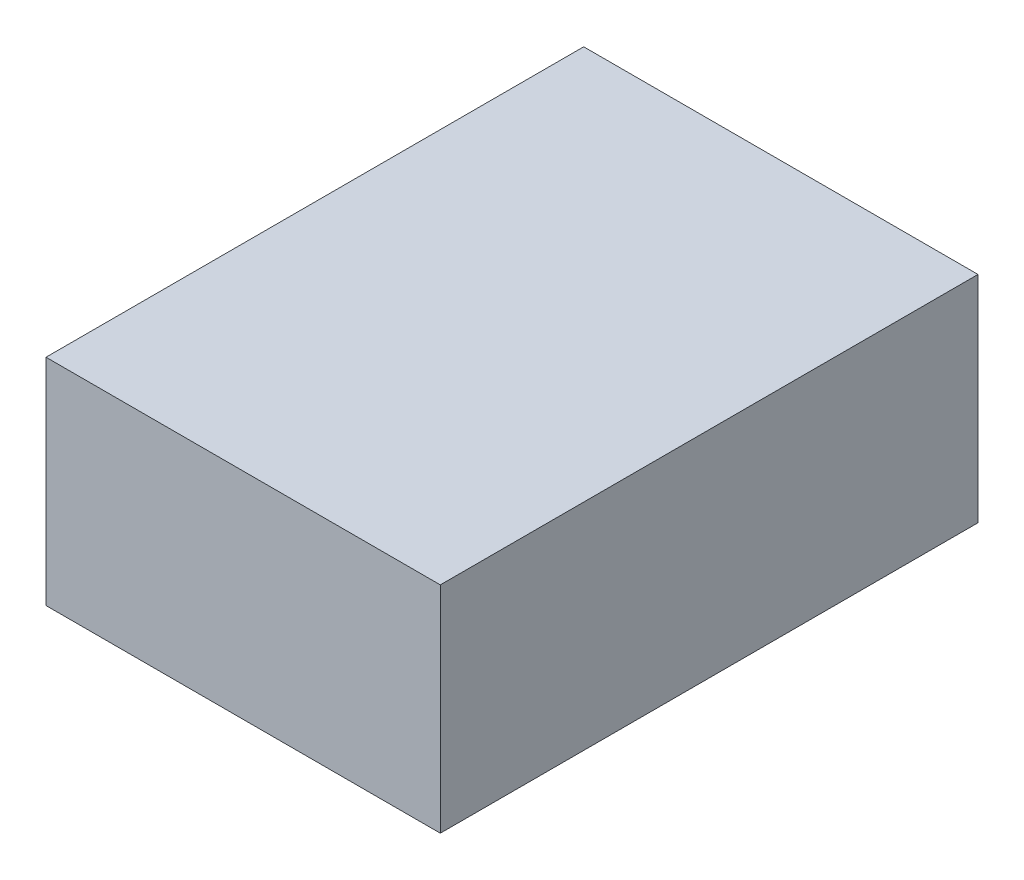
SolidWorks part; units mm, degrees
ref_plane "Plan de face" through (0, 0, 0) normal (0, 0, 1) x (1, 0, 0)
ref_plane "Plan de dessus" through (0, 0, 0) normal (0, 1, 0) x (1, 0, 0)
ref_plane "Plan de droite" through (0, 0, 0) normal (1, 0, 0) x (0, 0, -1)
sketch "Esquisse1" plane through (0, 0, 0) normal (0, 0, 1) x (1, 0, 0)
  line L1 (0, 0) -> (220, 0)
  line L2 (0, 0) -> (0, -120)
  line L3 (0, -120) -> (220, -120)
  line L4 (220, 0) -> (220, -120)
  dimension "D1" = 220
  dimension "D2" = 120
extrude "Boss.-Extru.1" add sketch "Esquisse1" along normal blind 300
